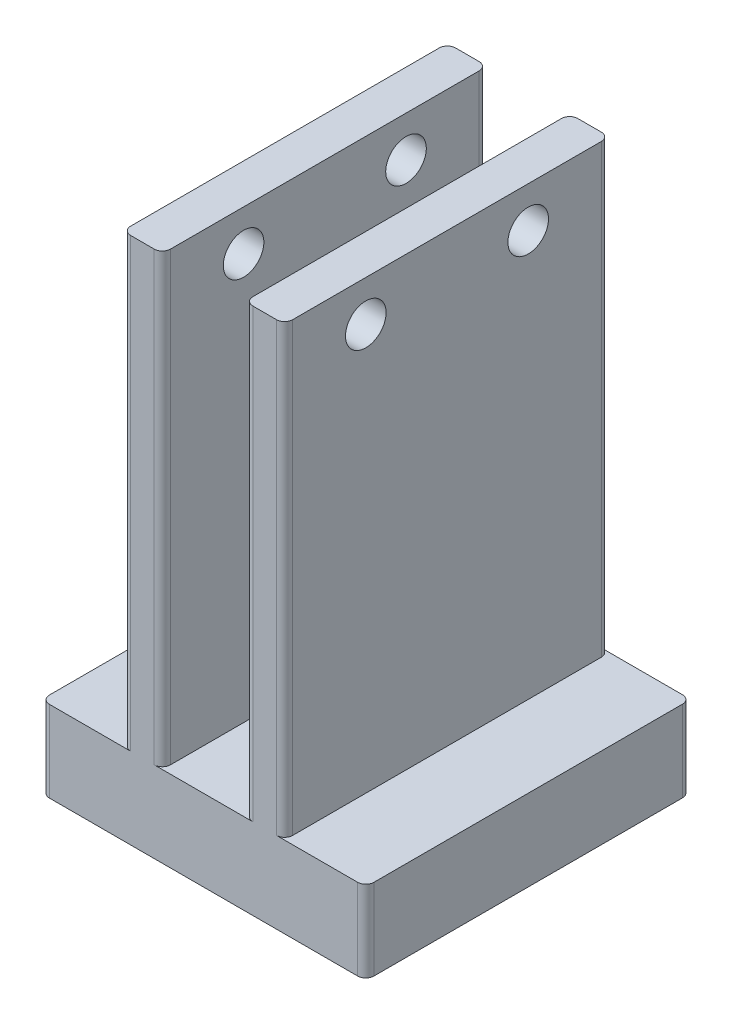
SolidWorks part; units mm, degrees
ref_plane "Front Plane" through (0, 0, 0) normal (0, 0, 1) x (1, 0, 0)
ref_plane "Top Plane" through (0, 0, 0) normal (0, 1, 0) x (1, 0, 0)
ref_plane "Right Plane" through (0, 0, 0) normal (1, 0, 0) x (0, 0, -1)
sketch "Sketch1" plane through (0, 0, 0) normal (0, 1, 0) x (1, 0, 0)
  line L1 (-12.5, 20) -> (-7.6, 20)
  line L2 (-12.5, 20) -> (-12.5, -20)
  line L3 (-12.5, -20) -> (-7.6, -20)
  line L4 (-7.6, 20) -> (-7.6, -20)
  line L5 (2.55, 20) -> (7.45, 20)
  line L6 (2.55, 20) -> (2.55, -20)
  line L7 (2.55, -20) -> (7.45, -20)
  line L8 (7.45, 20) -> (7.45, -20)
  point P9 (-7.6, 0)
  dimension "D1" = 4.9
  dimension "D2" = 40
  dimension "D3" = 10.15
  dimension "D4" = 2.55
extrude "Boss-Extrude1" add sketch "Sketch1" along normal blind 55
sketch "Sketch2" plane through (0, 0, 0) normal (0, -1, 0) x (1, 0, 0)
  line L1 (-12.5, 20) -> (7.45, 20)
  line L2 (-12.5, 20) -> (-12.5, -20)
  line L3 (-12.5, -20) -> (7.45, -20)
  line L4 (7.45, 20) -> (7.45, -20)
extrude "Boss-Extrude2" add sketch "Sketch2" along normal blind 10
sketch "Sketch3" plane through (-12.5, 0, 0) normal (-1, 0, 0) x (0, 0, 1)
  line L0 (-20, 55) -> (20, 55) construction
  circle A0 centre (-10, 50) radius 2.5
  circle A1 centre (10, 50) radius 2.5
  point P6 (0, 55)
  dimension "D1" = 5
  dimension "D2" = 5
  dimension "D3" = 5
  dimension "D4" = 5
  dimension "D5" = 10
  dimension "D6" = 10
extrude "Cut-Extrude1" cut sketch "Sketch3" against normal up to surface (19.95 mm away) up to face at (7.45, 22.5, 0)
sketch "Sketch5" plane through (-12.5, 0, 0) normal (-1, 0, 0) x (0, 0, 1)
  line L0 (20, 55) -> (20, -10) construction
  line L1 (-20, -10) -> (20, -10)
  line L2 (-20, -10) -> (-20, 0)
  line L3 (-20, 0) -> (20, 0)
  line L4 (20, -10) -> (20, 0)
  dimension "D1" = 10
extrude "Boss-Extrude4" add sketch "Sketch5" along normal blind 10
sketch "Sketch6" plane through (7.45, 0, 0) normal (1, 0, 0) x (0, 0, -1)
  line L0 (20, -10) -> (20, 55) construction
  line L1 (-20, -10) -> (20, -10)
  line L2 (-20, -10) -> (-20, 0)
  line L3 (-20, 0) -> (20, 0)
  line L4 (20, -10) -> (20, 0)
  dimension "D1" = 10
extrude "Boss-Extrude5" add sketch "Sketch6" along normal blind 10
fillet "Fillet1" radius 1 12 edges at (17.45, -5, -20) (-22.5, -5, -20) (-22.5, -5, 20) (17.45, -5, 20) (-7.6, 27.5, -20) (2.55, 27.5, -20) (2.55, 27.5, 20) (-7.6, 27.5, 20) (7.45, 27.5, 20) (-12.5, 27.5, 20) (-12.5, 27.5, -20) (7.45, 27.5, -20)
